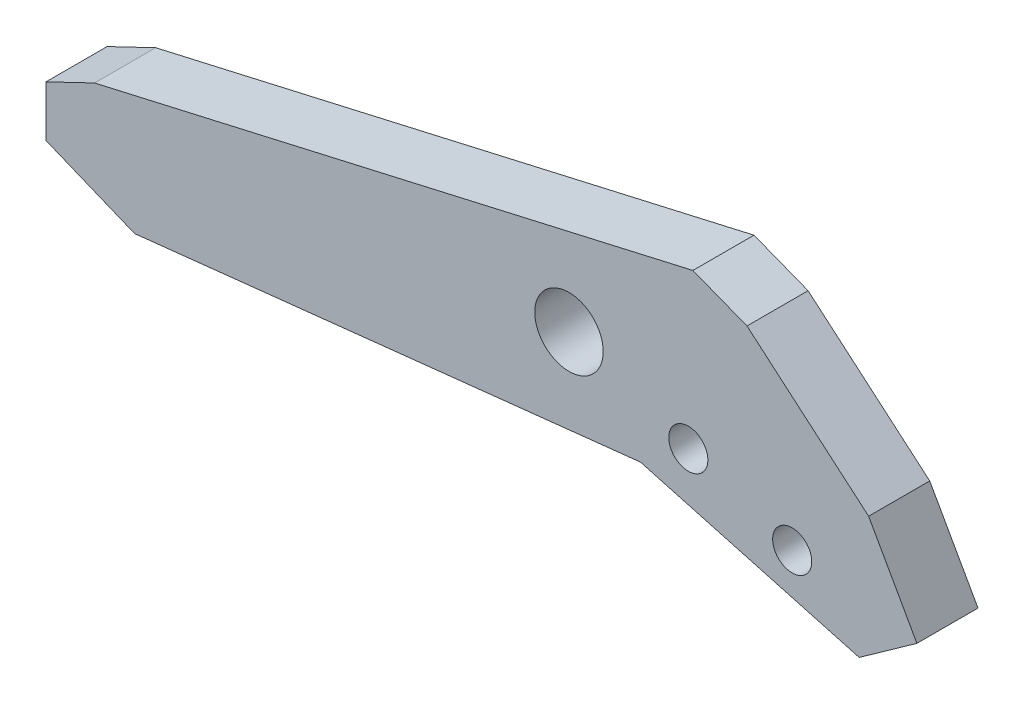
SolidWorks part; units mm, degrees
ref_plane "Front Plane" through (0, 0, 0) normal (0, 0, 1) x (1, 0, 0)
ref_plane "Top Plane" through (0, 0, 0) normal (0, 1, 0) x (1, 0, 0)
ref_plane "Right Plane" through (0, 0, 0) normal (1, 0, 0) x (0, 0, -1)
sketch "Sketch1" plane through (0, 0, 0) normal (0, 0, 1) x (1, 0, 0)
  line L0 (-22.225, 0) -> (22.225, 0) construction
  line L1 (0, 0) -> (0, 2.6037) construction
  line L2 (0, 5.715) -> (0, -5.715) construction
  line L3 (0, 0) -> (-5.183, 0) construction
  line L4 (14.2022, 7.2257) -> (20.523, 1.8256)
  line L5 (0, 5.715) -> (11.3915, 8.3198)
  line L6 (0, 5.715) -> (-19.7003, 1.2103)
  line L7 (-19.7003, 1.2103) -> (-22.225, 0)
  line L8 (-22.225, 0) -> (-22.225, -2.6437)
  line L9 (-22.225, -2.6437) -> (-17.6191, -4.5275)
  line L10 (-17.6191, -4.5275) -> (8.6667, -1.6682)
  line L11 (8.6667, -1.6682) -> (20.033, -4.7764)
  line L12 (20.033, -4.7764) -> (23.0314, -2.6437)
  line L13 (23.0314, -2.6437) -> (20.523, 1.8256)
  line L14 (11.3915, 8.3198) -> (14.2022, 7.2257)
  dimension "D1" = 44.45
  dimension "D2" = 11.43
extrude "Boss-Extrude1" add sketch "Sketch1" along normal blind 3.175
sketch "Sketch2" plane through (0, 0, 3.175) normal (0, 0, 1) x (1, 0, 0)
  circle A0 centre (11.1532, 0.1775) radius 1.016
  circle A1 centre (16.5512, -1.6996) radius 1.016
  circle A2 centre (4.9516, 2.334) radius 1.778
  dimension "D2" = 2.032
  dimension "D3" = 3.556
  dimension "D1" = 2.032
extrude "Cut-Extrude1" cut sketch "Sketch2" against normal through all
